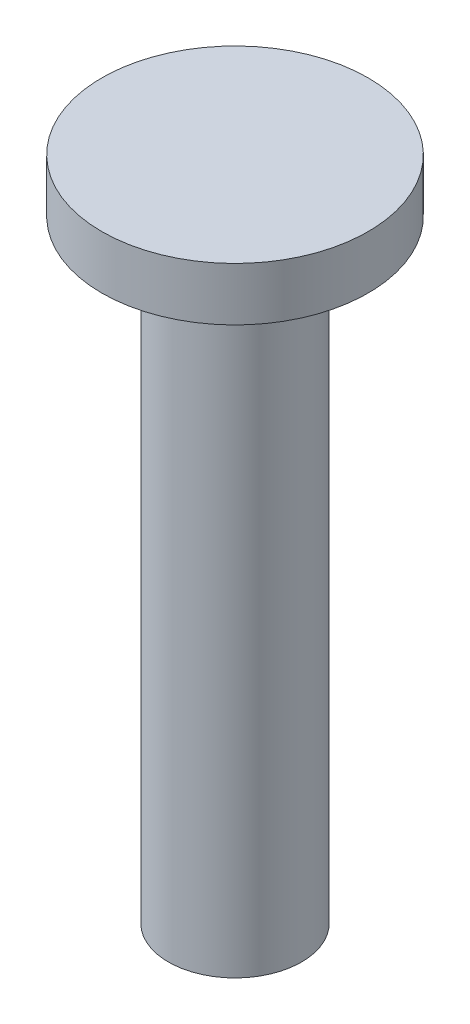
SolidWorks part; units mm, degrees
ref_plane "前视基准面" through (0, 0, 0) normal (0, 0, 1) x (1, 0, 0)
ref_plane "上视基准面" through (0, 0, 0) normal (0, 1, 0) x (1, 0, 0)
ref_plane "右视基准面" through (0, 0, 0) normal (1, 0, 0) x (0, 0, -1)
sketch "草图1" plane through (0, 0, 0) normal (0, 0, 1) x (1, 0, 0)
  line L0 (0, 0) -> (0, 24.8891) construction
  line L1 (0, 0) -> (-1, 0)
  line L2 (-1, 0) -> (-1, 9.2)
  line L3 (-1, 9.2) -> (-2, 9.2)
  line L4 (-2, 9.2) -> (-2, 10)
  line L5 (-2, 10) -> (0, 10)
  line L6 (0, 10) -> (0, 0)
  dimension "D1" = 0.8
  dimension "D2" = 4
  dimension "D3" = 2
  dimension "D4" = 10
revolve "旋转1" add sketch "草图1" angle 360 about L0
